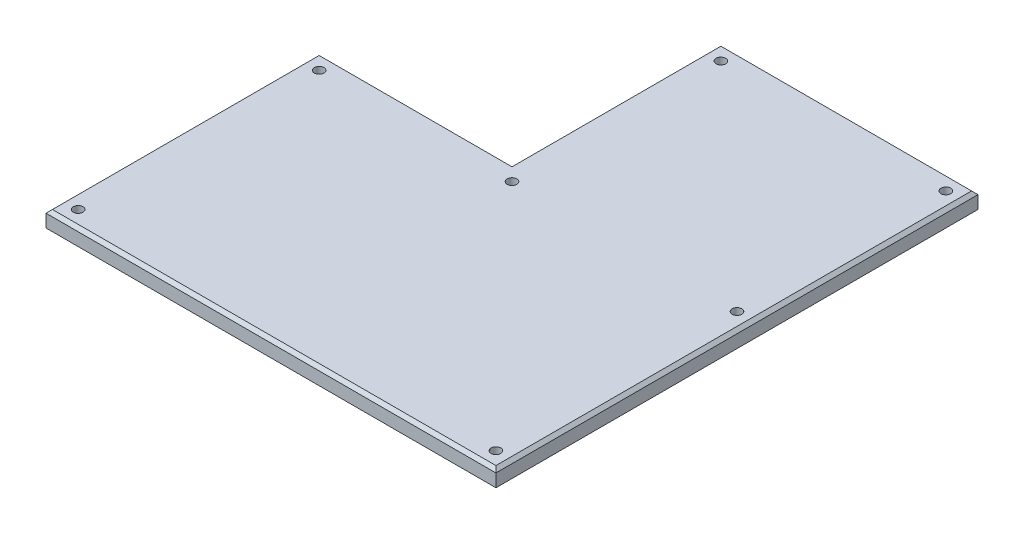
SolidWorks part; units mm, degrees
ref_plane "Front Plane" through (0, 0, 0) normal (0, 0, 1) x (1, 0, 0)
ref_plane "Top Plane" through (0, 0, 0) normal (0, 1, 0) x (1, 0, 0)
ref_plane "Right Plane" through (0, 0, 0) normal (1, 0, 0) x (0, 0, -1)
sketch "Sketch1" plane through (0, 0, 0) normal (0, 1, 0) x (1, 0, 0)
  line L0 (140, 150) -> (140, 0)
  line L1 (0, 0) -> (140, 0)
  line L2 (0, 0) -> (0, 85)
  line L3 (0, 85) -> (60, 85)
  line L6 (60, 85) -> (60, 150)
  line L7 (60, 150) -> (140, 150)
  dimension "D2" = 150
  dimension "D3" = 140
  dimension "D4" = 85
  dimension "D8" = 80
extrude "Boss-Extrude1" add sketch "Sketch1" along normal blind 5
chamfer "Chamfer1" distance 1 angle 45 6 edges at (140, 5, -75) (100, 5, -150) (60, 5, -117.5) (30, 5, -85) (0, 5, -42.5) (70, 5, 0)
sketch "Sketch2" plane through (0, 5, 0) normal (0, 1, 0) x (1, 0, 0)
  line L0 (0, 0) -> (0, 85) construction
  line L1 (0, 85) -> (60, 85) construction
  circle A0 centre (5, 80) radius 1.5
  dimension "D1" = 3
  dimension "D2" = 5
  dimension "D3" = 5
extrude "Cut-Extrude1" cut sketch "Sketch2" against normal blind 5
pattern_linear "LPattern1" count 2 spacing 130 along (1, 0, 0) count 2 spacing 75 along (0, 0, 1) of "Cut-Extrude1"
sketch "Sketch3" plane through (0, 5, 0) normal (0, 1, 0) x (1, 0, 0)
  line L0 (60, 85) -> (60, 150) construction
  line L1 (60, 150) -> (140, 150) construction
  circle A0 centre (65, 145) radius 1.5
  dimension "D1" = 3
  dimension "D2" = 5
  dimension "D3" = 5
extrude "Cut-Extrude2" cut sketch "Sketch3" against normal blind 5
pattern_linear "LPattern2" count 2 spacing 70 along (1, 0, 0) of "Cut-Extrude2"
pattern_linear "LPattern3" count 2 spacing 65 along (0, 0, 1) of "Cut-Extrude2"
